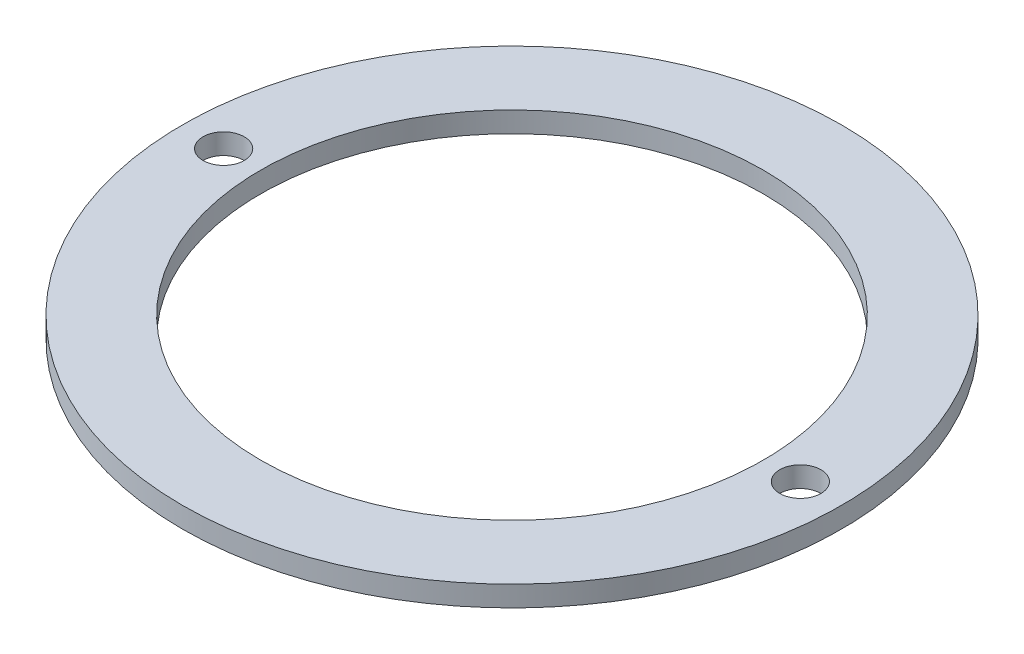
SolidWorks part; units mm, degrees
ref_plane "Front Plane" through (0, 0, 0) normal (0, 0, 1) x (1, 0, 0)
ref_plane "Top Plane" through (0, 0, 0) normal (0, 1, 0) x (1, 0, 0)
ref_plane "Right Plane" through (0, 0, 0) normal (1, 0, 0) x (0, 0, -1)
sketch "Sketch1" plane through (0, 0, 0) normal (0, 1, 0) x (1, 0, 0)
  circle A0 centre (0, 0) radius 8
  dimension "D1" = 16
extrude "Boss-Extrude1" add sketch "Sketch1" along normal blind 0.5
sketch "Sketch2" plane through (0, 0.5, 0) normal (0, 1, 0) x (1, 0, 0)
  circle A0 centre (0, 0) radius 6.1
  dimension "D1" = 12.2
extrude "Cut-Extrude1" cut sketch "Sketch2" against normal through all
hole_wizard "Ø1.0 (1) Diameter Hole1" positions "Sketch7" profile "Sketch6" hole size "Ø1.0" standard "DIN" end condition up to next
sketch "Sketch7" plane through (0, 0.5, 0) normal (0, 1, 0) x (1, 0, 0)
  circle A0 centre (0, 0) radius 7 construction
  point P4 (-7, 0)
  point P6 (7, 0)
  dimension "D1" = 14
sketch "Sketch6" plane through (-7, 0.5, 0) normal (1, 0, 0) x (0, 0, 1)
  line L0 (0, 0) -> (0, 0.5)
  line L1 (0, 0.5) -> (0.5, 0.5)
  line L2 (0.5, 0.5) -> (0.5, 0)
  line L5 (0.5, 0) -> (0, 0)
  line L11 (0, -6.35) -> (0, 107.95) construction
  dimension "Thru Hole Dia." = 1
  dimension "Thru Hole Depth" = 0.5
